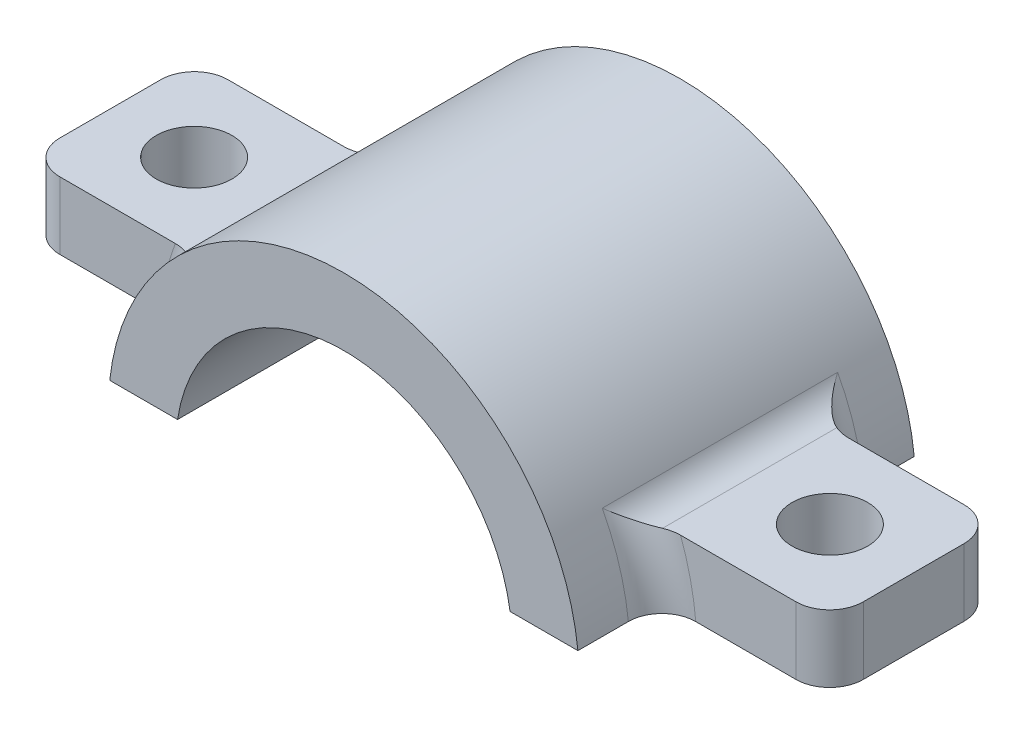
SolidWorks part; units mm, degrees
ref_plane "Front Plane" through (0, 0, 0) normal (0, 0, 1) x (1, 0, 0)
ref_plane "Top Plane" through (0, 0, 0) normal (0, 1, 0) x (1, 0, 0)
ref_plane "Right Plane" through (0, 0, 0) normal (1, 0, 0) x (0, 0, -1)
sketch "Sketch1" plane through (0, 0, 0) normal (0, 0, 1) x (1, 0, 0)
  line L0 (-20.9241, 0) -> (19.9256, 0) construction
  line L1 (-13.9194, 1.5) -> (-9.8869, 1.5)
  line L2 (9.8869, 1.5) -> (13.9194, 1.5)
  arc A0 (-9.8869, 1.5) -> (9.8869, 1.5) centre (0, 0) cw
  arc A1 (-13.9194, 1.5) -> (13.9194, 1.5) centre (0, 0) cw
  dimension "D1" = 10
  dimension "D3" = 14
  dimension "D2" = 1.5
extrude "Boss-Extrude1" add sketch "Sketch1" along normal mid plane 20
sketch "Sketch2" plane through (0, 1.5, 0) normal (0, -1, 0) x (1, 0, 0)
  line L0 (-22.5419, 0) -> (38.0452, 0) construction
  line L1 (9.8869, 10) -> (9.8869, -10) construction
  line L2 (9.8869, 5) -> (23.8869, 5)
  line L3 (9.8869, 5) -> (9.8869, -5)
  line L4 (9.8869, -5) -> (23.8869, -5)
  line L5 (23.8869, 5) -> (23.8869, -5)
  line L6 (23.8869, -5) -> (13.9194, 5) construction
  line L7 (13.9194, 10) -> (13.9194, -10) construction
  line L8 (23.8869, 5) -> (13.9194, -5) construction
  line L9 (0, 23.1939) -> (0, -22.8481) construction
  line L10 (-9.8869, -5) -> (-23.8869, -5)
  line L11 (-23.8869, 5) -> (-23.8869, -5)
  line L12 (-9.8869, 5) -> (-23.8869, 5)
  line L13 (-9.8869, 5) -> (-9.8869, -5)
  circle A0 centre (18.9031, 0) radius 2.25
  circle A1 centre (-18.9031, 0) radius 2.25
  dimension "D3" = 4.5
  dimension "D1" = 10
  dimension "D2" = 14
extrude "Boss-Extrude2" add sketch "Sketch2" against normal blind 4
fillet "Fillet1" radius 2 10 edges at (12.8744, 5.5, 0) (13.5454, 3.5388, 5) (13.5454, 3.5388, -5) (-12.8744, 5.5, 0) (-13.5454, 3.5388, 5) (-13.5454, 3.5388, -5) (-23.8869, 3.5, -5) (-23.8869, 3.5, 5) (23.8869, 3.5, 5) (23.8869, 3.5, -5)
